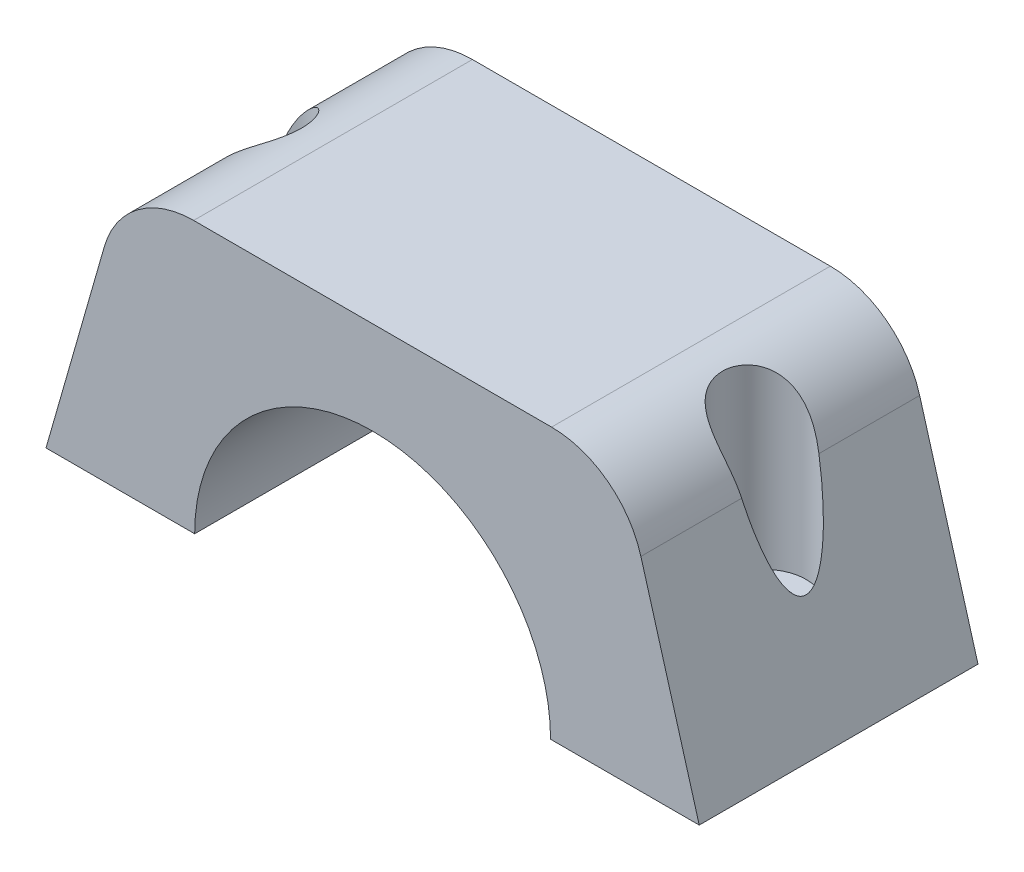
SolidWorks part; units mm, degrees
ref_plane "Front Plane" through (0, 0, 0) normal (0, 0, 1) x (1, 0, 0)
ref_plane "Top Plane" through (0, 0, 0) normal (0, 1, 0) x (1, 0, 0)
ref_plane "Right Plane" through (0, 0, 0) normal (1, 0, 0) x (0, 0, -1)
sketch "Sketch1" plane through (0, 0, 0) normal (0, 0, 1) x (1, 0, 0)
  line L0 (-35.15, 0) -> (35.15, 0) construction
  line L1 (-35.15, 0) -> (-26.7971, 29.15)
  line L2 (-26.7971, 29.15) -> (26.7971, 29.15)
  line L3 (0, 29.15) -> (0, 0) construction
  line L4 (35.15, 0) -> (26.7971, 29.15)
  line L6 (-35.15, 0) -> (-19.15, 0)
  line L7 (19.15, 0) -> (35.15, 0)
  circle A1 centre (0, 0) radius 19.15
  point P11 (0, 19.15)
  dimension "D1" = 10
extrude "Boss-Extrude1" add sketch "Sketch1" along normal blind 30 contours A1 L7 L4 L2 L1 L6
fillet "Fillet1" radius 10 2 edges at (26.7971, 29.15, 15) (-26.7971, 29.15, 15)
sketch "Sketch2" plane through (0, 0, 0) normal (0, -1, 0) x (1, 0, 0)
  line L0 (0, 0) -> (0, 30) construction
  line L1 (19.15, 30) -> (-19.15, 30) construction
  line L2 (-35.15, 30) -> (-19.15, 30) construction
  circle A0 centre (-27.15, 15) radius 2.5
  circle A1 centre (27.15, 15) radius 2.5
  point P8 (0, 15)
  point P12 (-27.15, 30)
  dimension "D1" = 5
extrude "Cut-Extrude1" cut sketch "Sketch2" against normal through all
sketch "Sketch3" plane through (0, 29.15, 0) normal (0, 1, 0) x (1, 0, 0)
  line L0 (0, 0) -> (0, -30) construction
  line L1 (-19.2601, -30) -> (19.2601, -30) construction
  arc A0 (28.8732, -13.1888) -> (28.8732, -16.8112) centre (27.15, -15) ccw construction
  arc A1 (28.8732, -13.1888) -> (28.8732, -16.8112) centre (27.15, -15) ccw
  circle A2 centre (27.15, -15) radius 4.5
  circle A3 centre (-27.15, -15) radius 4.5
  dimension "D1" = 9
extrude "Cut-Extrude2" cut sketch "Sketch3" against normal blind 20
